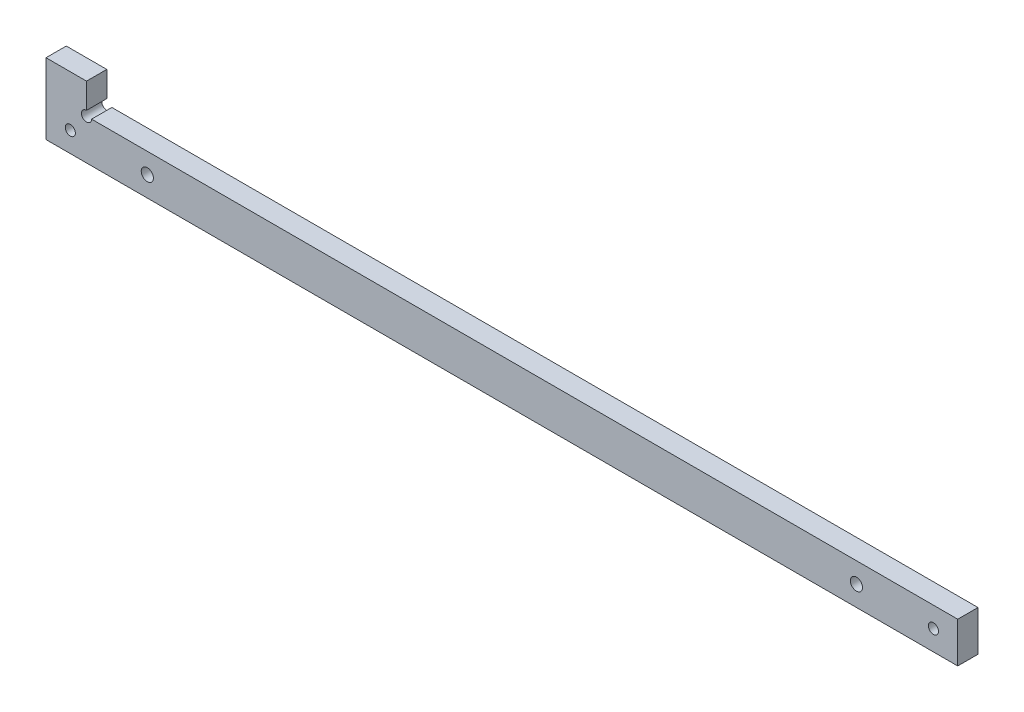
SolidWorks part; units mm, degrees
ref_plane "Front Plane" through (0, 0, 0) normal (0, 0, 1) x (1, 0, 0)
ref_plane "Top Plane" through (0, 0, 0) normal (0, 1, 0) x (1, 0, 0)
ref_plane "Right Plane" through (0, 0, 0) normal (1, 0, 0) x (0, 0, -1)
sketch "Sketch1" plane through (0, 0, 0) normal (0, 0, 1) x (1, 0, 0)
  line L0 (0, 15) -> (0, 2.5)
  line L1 (2.5, 0) -> (430, 0)
  line L2 (430, 0) -> (430, -20)
  line L3 (430, -20) -> (-20, -20)
  line L4 (-20, -20) -> (-20, 15)
  line L5 (-20, 15) -> (0, 15)
  arc A0 (0, 2.5) -> (2.5, 0) centre (0, 0) ccw
  dimension "D1" = 5
  dimension "D2" = 20
  dimension "D3" = 15
  dimension "D4" = 20
  dimension "D5" = 430
extrude "Boss-Extrude1" add sketch "Sketch1" along normal blind 10
sketch "Sketch3" plane through (0, 0, 10) normal (0, 0, 1) x (1, 0, 0)
  line L0 (459.0002, -10) -> (-116.6065, -10) construction
  line L1 (-20, 15) -> (-20, -20) construction
  line L2 (430, -20) -> (430, 0) construction
  circle A0 centre (30, -10) radius 3
  circle A1 centre (380, -10) radius 3
  circle A2 centre (-8, -10) radius 2.5
  circle A3 centre (418, -10) radius 2.5
  dimension "D1" = 6
  dimension "D2" = 6
  dimension "D5" = 5
  dimension "D3" = 50
  dimension "D4" = 50
  dimension "D6" = 12
  dimension "D7" = 38
  dimension "D8" = 38
extrude "Cut-Extrude2" cut sketch "Sketch3" against normal through all
sketch "Sketch4" plane through (0, 0, 0) normal (0, 0, -1) x (-1, 0, 0)
  line L0 (-438.419, -10) -> (52.5801, -10) construction
  line L1 (-418, -10) -> (-418, -3.6752) construction
  line L2 (-380, -10) -> (-380, -2.7516) construction
  line L3 (-30, -10) -> (-30, -3.6752) construction
  line L4 (8, -10) -> (8, -15.2052) construction
  line L5 (8, -10) -> (8, -3.6752) construction
  line L6 (-30, -10) -> (-30, -18.1441) construction
  line L7 (-380, -10) -> (-380, -18.1441) construction
  line L8 (-418, -10) -> (-418, -18.1441) construction
